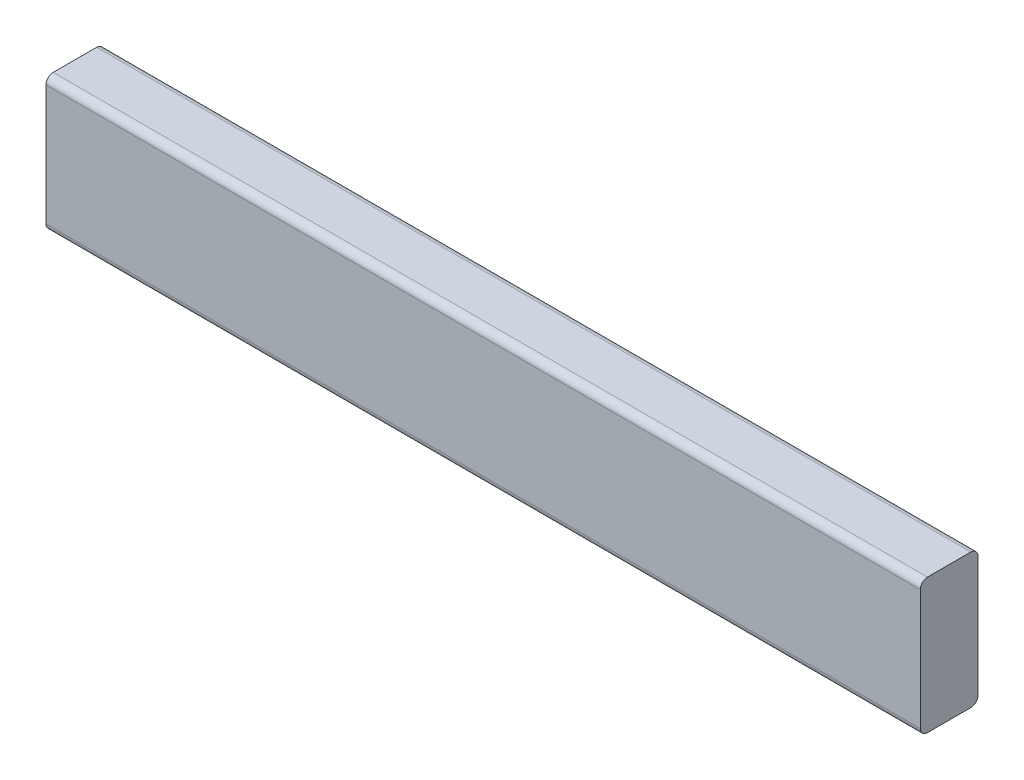
SolidWorks part; units mm, degrees
material "Pine"
ref_plane "Front Plane" through (0, 0, 0) normal (0, 0, 1) x (1, 0, 0)
ref_plane "Top Plane" through (0, 0, 0) normal (0, 1, 0) x (1, 0, 0)
ref_plane "Right Plane" through (0, 0, 0) normal (1, 0, 0) x (0, 0, -1)
sketch "Sketch1" plane through (0, 0, 0) normal (0, 0, 1) x (1, 0, 0)
  line L1 (-781.7306, 88.9) -> (-204.9322, 88.9)
  line L2 (-781.7306, 88.9) -> (-781.7306, 0)
  line L3 (-781.7306, 0) -> (-204.9322, 0)
  line L4 (-204.9322, 88.9) -> (-204.9322, 0)
extrude "Boss-Extrude1" add sketch "Sketch1" against normal up to surface (38.1 mm away)
fillet "Fillet1" radius 4.7625 4 edges at (-493.3314, 0, -38.1) (-493.3314, 0, 0) (-493.3314, 88.9, -38.1) (-493.3314, 88.9, 0)
